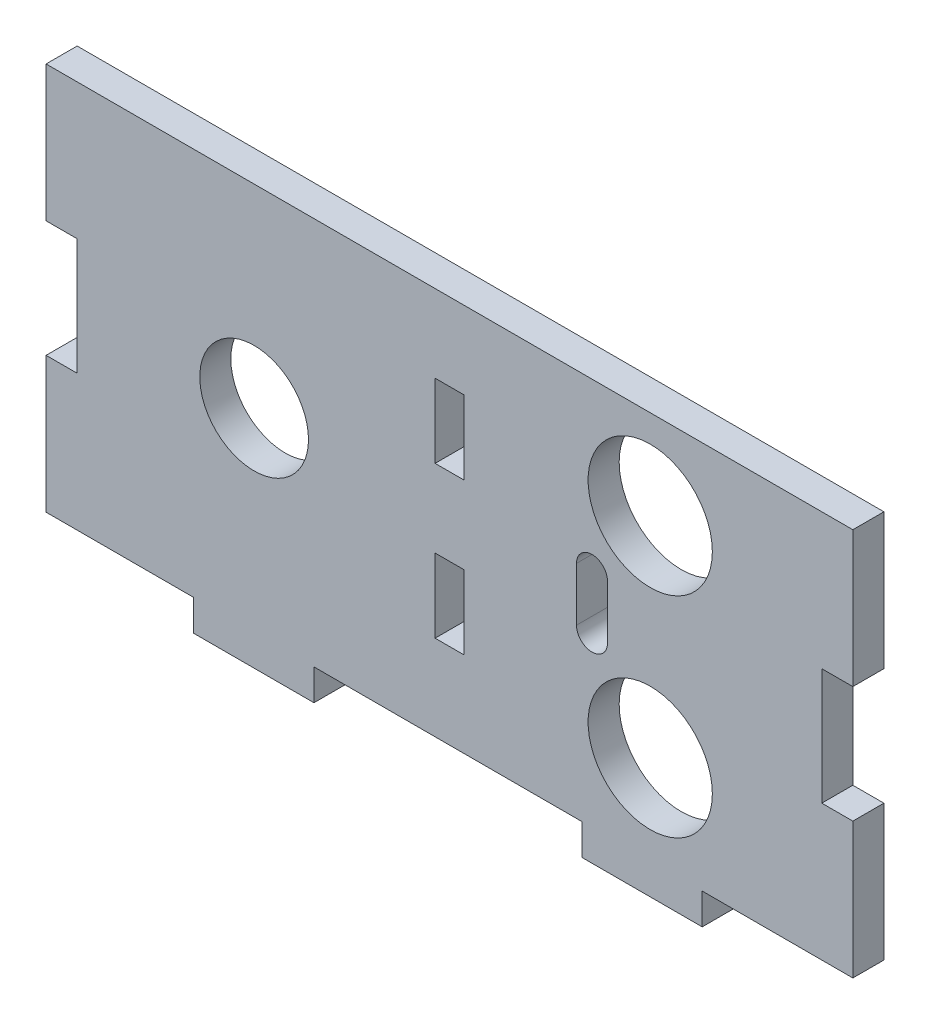
SolidWorks part; units mm, degrees
ref_plane "Ebene vorne" through (0, 0, 0) normal (0, 0, 1) x (1, 0, 0)
ref_plane "Ebene oben" through (0, 0, 0) normal (0, 1, 0) x (1, 0, 0)
ref_plane "Ebene rechts" through (0, 0, 0) normal (1, 0, 0) x (0, 0, -1)
sketch "Skizze1" plane through (0, 0, 0) normal (0, 0, 1) x (1, 0, 0)
  line L1 (0, 0) -> (200, 0)
  line L2 (0, 0) -> (0, 50)
  line L3 (0, 50) -> (200, 50)
  line L4 (200, 0) -> (200, 50)
  dimension "D1" = 200
  dimension "D2" = 50
extrude "Aufsatz-Linear austragen1" add sketch "Skizze1" along normal blind 4
sketch "Skizze2" plane through (0, 0, 4) normal (0, 0, -1) x (-1, 0, 0)
  line L0 (0, 0) -> (-200, 0) construction
  line L1 (-182.55, 0) -> (-167.05, 0)
  line L2 (-182.55, 0) -> (-182.55, -4)
  line L3 (-182.55, -4) -> (-167.05, -4)
  line L4 (-167.05, 0) -> (-167.05, -4)
  line L5 (-200, 0) -> (-200, 50) construction
  line L6 (-132.55, 0) -> (-117.05, 0)
  line L7 (-132.55, 0) -> (-132.55, -4)
  line L8 (-132.55, -4) -> (-117.05, -4)
  line L9 (-117.05, 0) -> (-117.05, -4)
  line L10 (-82.55, 0) -> (-67.05, 0)
  line L11 (-82.55, 0) -> (-82.55, -4)
  line L12 (-82.55, -4) -> (-67.05, -4)
  line L13 (-67.05, 0) -> (-67.05, -4)
  line L14 (-32.55, 0) -> (-17.05, 0)
  line L15 (-32.55, 0) -> (-32.55, -4)
  line L16 (-32.55, -4) -> (-17.05, -4)
  line L17 (-17.05, 0) -> (-17.05, -4)
  line L22 (17.45, 0) -> (32.95, 0) [skipped]
  line L23 (17.45, 0) -> (17.45, -4) [skipped]
  line L24 (17.45, -4) -> (32.95, -4) [skipped]
  line L25 (32.95, 0) -> (32.95, -4) [skipped]
  dimension "D1" = 15.5
  dimension "D2" = 17.45
  dimension "D3" = 4
  dimension "D4" = 5
extrude "Aufsatz-Linear austragen2" add sketch "Skizze2" along normal blind 4
sketch "Skizze4" plane through (0, 0, 4) normal (0, 0, 1) x (1, 0, 0)
  line L0 (0, 50) -> (0, 0) construction
  line L1 (0, 32.5) -> (4, 32.5)
  line L2 (0, 32.5) -> (0, 17.5)
  line L3 (0, 17.5) -> (4, 17.5)
  line L4 (4, 32.5) -> (4, 17.5)
  line L5 (200, 50) -> (0, 50) construction
  line L6 (100, 50) -> (100, -17.3733) construction
  line L7 (196, 32.5) -> (196, 17.5)
  line L8 (200, 17.5) -> (196, 17.5)
  line L9 (200, 32.5) -> (200, 17.5)
  line L10 (200, 32.5) -> (196, 32.5)
  dimension "D1" = 4
  dimension "D2" = 15
  dimension "D3" = 17.5
extrude "Schnitt-Linear austragen1" cut sketch "Skizze4" against normal up to next
sketch "Skizze5" plane through (0, 0, 0) normal (0, 0, -1) x (-1, 0, 0)
  line L0 (-101.85, 40) -> (-101.85, 30.5)
  line L1 (-101.85, 30.5) -> (-98.15, 30.5)
  line L2 (-98.15, 30.5) -> (-98.15, 40)
  line L3 (-98.15, 40) -> (-101.85, 40)
  line L5 (-200, 50) -> (0, 50) construction
  line L6 (-100, 110.8331) -> (-100, -10.8331) construction
  line L7 (-101.85, 20.5) -> (-98.15, 20.5)
  line L8 (-101.85, 20.5) -> (-101.85, 11)
  line L9 (-101.85, 11) -> (-98.15, 11)
  line L10 (-98.15, 20.5) -> (-98.15, 11)
  line L11 (-100, 40) -> (-100, 5.6222) construction
  line L12 (-200, 50) -> (0, 50) construction
  point P16 (-100, 50)
  dimension "D1" = 3.7
  dimension "D2" = 9.5
  dimension "D4" = 10
  dimension "D5" = 10
extrude "Schnitt-Linear austragen2" cut sketch "Skizze5" against normal up to next
sketch "Skizze6" plane through (0, 0, 4) normal (0, 0, 1) x (1, 0, 0)
  line L0 (100, 74.3836) -> (100, -34.9154) construction
  line L1 (200, 32.5) -> (200, 50) construction
  line L2 (0, 50) -> (0, 32.5) construction
  line L3 (52.05, 32.5) -> (48.05, 32.5)
  line L4 (48.05, 66.1416) -> (-25.3013, 66.1416)
  line L6 (48.05, -17.0714) -> (-25.3013, -17.0714)
  line L7 (-25.3013, 66.1416) -> (-25.3013, -17.0714)
  line L9 (48.05, 17.5) -> (52.05, 17.5)
  line L10 (-61.8058, 25) -> (218.4998, 25) construction
  line L11 (132.55, 0) -> (167.05, 0) construction
  line L12 (200, 50) -> (0, 50) construction
  line L14 (48.05, 32.5) -> (48.05, 66.1416)
  line L15 (48.05, 17.5) -> (48.05, -17.0714)
  line L17 (52.05, 17.5) -> (52.05, 32.5)
  line L19 (52.05, -4) -> (52.05, 0) construction
  dimension "D1" = 15
  dimension "D2" = 4
extrude "Schnitt-Linear austragen3" cut sketch "Skizze6" against normal up to next (4 mm away)
ref_plane "Ebene1" through (100, 0, 0) normal (-1, 0, 0) x (0, 0, 1)
mirror "Spiegeln1" about plane through (100, 0, 0) normal (-1, 0, 0) of "Schnitt-Linear austragen3"
sketch "Skizze7" plane through (0, 0, 4) normal (0, 0, 1) x (1, 0, 0)
  line L0 (118.3549, 28.449) -> (118.3549, 21.551) construction
  line L1 (120.3549, 28.449) -> (120.3549, 21.551)
  line L2 (116.3549, 28.449) -> (116.3549, 21.551)
  line L3 (191.437, 25) -> (20.3945, 25) construction
  line L4 (132.55, 0) -> (151.95, 0) construction
  line L5 (151.95, 50) -> (48.05, 50) construction
  circle A0 centre (125.8555, 11.5) radius 8
  circle A1 centre (125.8555, 38.5) radius 8
  arc A2 (120.3549, 28.449) -> (116.3549, 28.449) centre (118.3549, 28.449) ccw
  arc A3 (116.3549, 21.551) -> (120.3549, 21.551) centre (118.3549, 21.551) ccw
  circle A4 centre (74.8422, 25) radius 7
  point P4 (118.3549, 25)
  dimension "D1" = 16
  dimension "D4" = 14
  dimension "D2" = 27
  dimension "D3" = 4
extrude "Schnitt-Linear austragen4" cut sketch "Skizze7" against normal up to next
